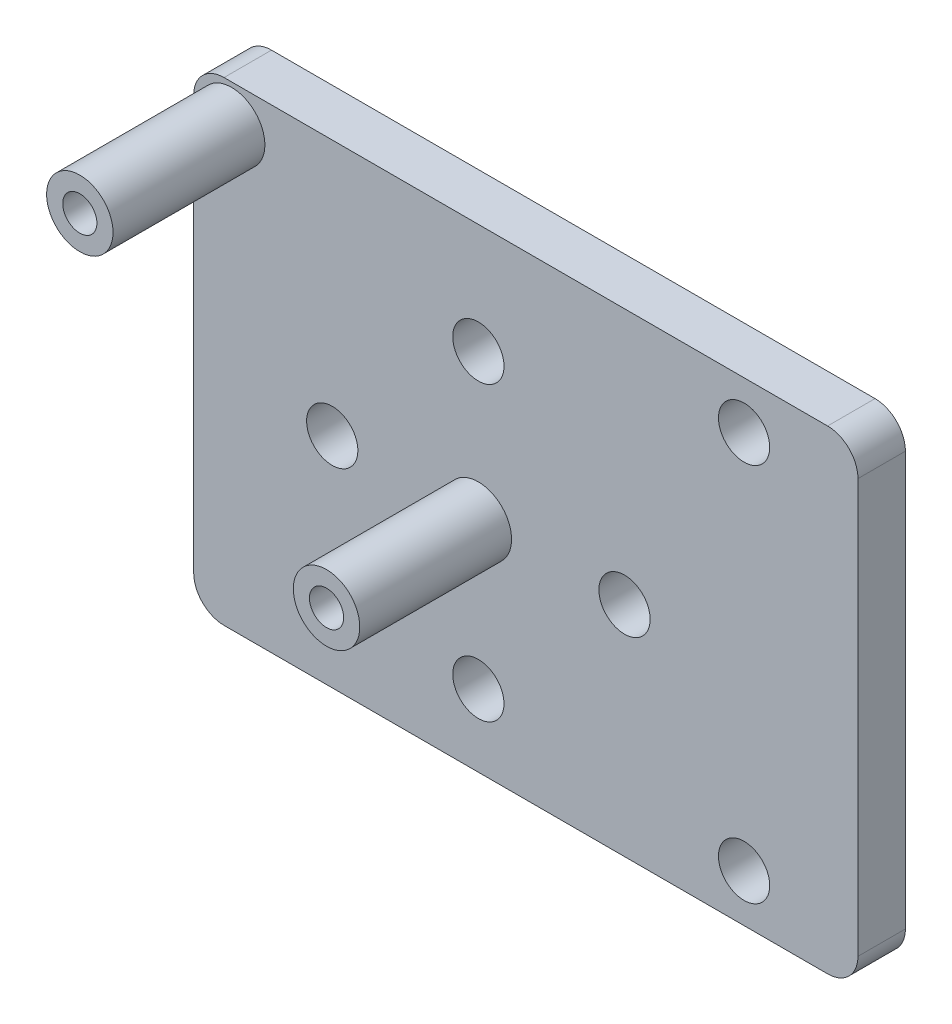
SolidWorks part; units mm, degrees
material "Copper"
ref_plane "Front Plane" through (0, 0, 0) normal (0, 0, 1) x (1, 0, 0)
ref_plane "Top Plane" through (0, 0, 0) normal (0, 1, 0) x (1, 0, 0)
ref_plane "Right Plane" through (0, 0, 0) normal (1, 0, 0) x (0, 0, -1)
sketch "Sketch1" plane through (0, 0, 0) normal (0, 0, 1) x (1, 0, 0)
  line L1 (0, 0) -> (-44.45, 0)
  line L2 (0, 0) -> (0, -31.75)
  line L3 (0, -31.75) -> (-44.45, -31.75)
  line L4 (-44.45, 0) -> (-44.45, -31.75)
  dimension "D1" = 31.75
  dimension "D2" = 44.45
extrude "Boss-Extrude1" add sketch "Sketch1" along normal blind 3.175
sketch "Sketch2" plane through (0, 0, 3.175) normal (0, 0, 1) x (1, 0, 0)
  line L0 (-44.45, 0) -> (-44.45, -31.75) construction
  line L1 (0, 0) -> (-44.45, 0) construction
  circle A0 centre (-41.91, -2.54) radius 2.2225
  circle A1 centre (-25.4, -17.145) radius 2.2225
  circle A2 centre (-25.4, -17.145) radius 1.143
  circle A3 centre (-41.91, -2.54) radius 1.143
  dimension "D1" = 16.51
  dimension "D3" = 2.286
  dimension "D4" = 2.286
  dimension "D5" = 4.445
  dimension "D6" = 4.445
  dimension "D2" = 14.605
  dimension "D7" = 19.05
  dimension "D8" = 2.54
extrude "Boss-Extrude2" add sketch "Sketch2" along normal blind 10.16
sketch "Sketch3" plane through (0, 0, 3.175) normal (0, 0, 1) x (1, 0, 0)
  line L0 (-44.45, -31.75) -> (0, -31.75) construction
  line L1 (0, -31.75) -> (0, 0) construction
  circle A0 centre (-7.62, -3.175) radius 1.7145
  circle A1 centre (-7.62, -28.575) radius 1.7145
  dimension "D1" = 3.429
  dimension "D2" = 3.429
  dimension "D3" = 25.4
  dimension "D4" = 3.175
  dimension "D5" = 7.62
  dimension "D6" = 7.62
extrude "Cut-Extrude1" cut sketch "Sketch3" against normal blind 12.7
sketch "Sketch4" plane through (0, 0, 3.175) normal (0, 0, 1) x (1, 0, 0)
  line L0 (-44.45, 0) -> (-44.45, -31.75) construction
  circle A0 centre (-25.4, -7.366) radius 1.7145
  circle A4 centre (-25.4, -17.145) radius 2.2225 construction
  dimension "D1" = 3.429
  dimension "D2" = 9.779
  dimension "D3" = 19.05
extrude "Cut-Extrude2" cut sketch "Sketch4" against normal blind 12.7
pattern_circular "CirPattern1" count 4 over 360 about axis through (-25.4, -17.145, 0) along (0, 0, 1) of "Cut-Extrude2"
fillet "Fillet1" radius 2.032 4 edges at (-44.45, 0, 1.5875) (-44.45, -31.75, 1.5875) (0, 0, 1.5875) (0, -31.75, 1.5875)
